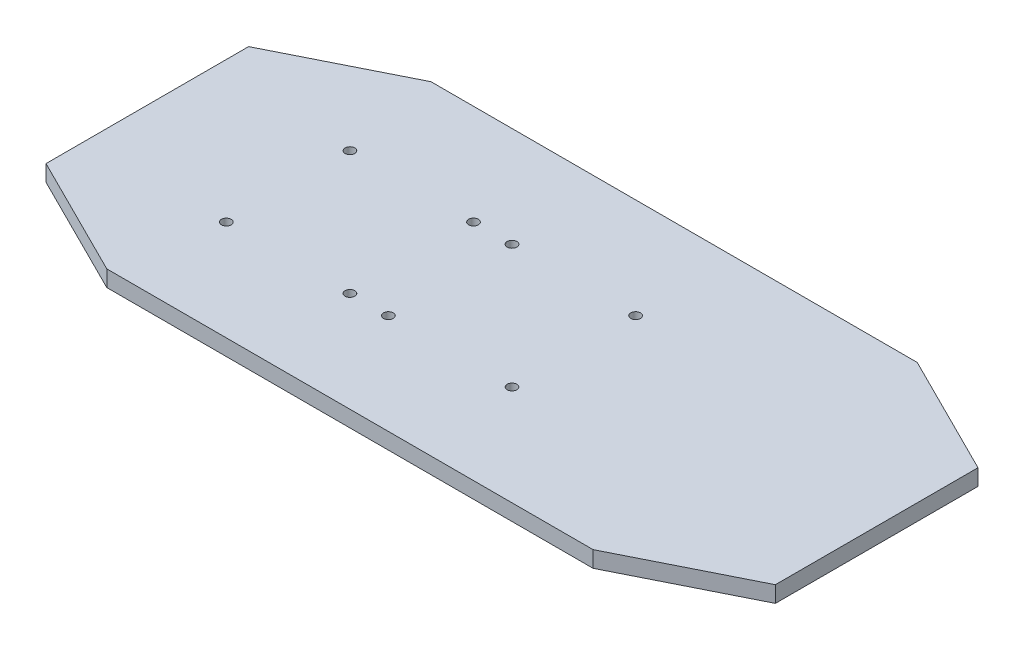
SolidWorks part; units mm, degrees
material "Pin"
ref_plane "Plan de face" through (0, 0, 0) normal (0, 0, 1) x (1, 0, 0)
ref_plane "Plan de dessus" through (0, 0, 0) normal (0, 1, 0) x (1, 0, 0)
ref_plane "Plan de droite" through (0, 0, 0) normal (1, 0, 0) x (0, 0, -1)
sketch "Esquisse1" plane through (0, 0, 0) normal (0, 1, 0) x (1, 0, 0)
  line L1 (0, 0) -> (180, 0)
  line L2 (0, 0) -> (0, 80)
  line L3 (0, 80) -> (180, 80)
  line L4 (180, 0) -> (180, 80)
  dimension "D1" = 180
  dimension "D2" = 80
extrude "Boss.-Extru.1" add sketch "Esquisse1" along normal blind 4
sketch "Esquisse2" plane through (0, 4, 0) normal (0, 1, 0) x (1, 0, 0)
  line L0 (0, 15) -> (30, 0)
  line L1 (0, 80) -> (0, 0) construction
  line L2 (0, 0) -> (180, 0) construction
  line L3 (30, 0) -> (0, 0)
  line L4 (0, 0) -> (0, 15)
  line L5 (30, 80) -> (0, 65)
  line L6 (180, 80) -> (0, 80) construction
  line L7 (0, 65) -> (0, 80)
  line L8 (0, 80) -> (30, 80)
  line L9 (150, 80) -> (180, 80)
  line L10 (180, 80) -> (180, 65)
  line L11 (180, 0) -> (180, 80) construction
  line L12 (180, 65) -> (150, 80)
  line L13 (180, 15) -> (150, 0)
  line L14 (150, 0) -> (180, 0)
  line L15 (180, 0) -> (180, 15)
  dimension "D1" = 30
  dimension "D2" = 15
  dimension "D3" = 30
  dimension "D4" = 15
  dimension "D5" = 15
  dimension "D6" = 30
  dimension "D7" = 30
  dimension "D8" = 15
extrude "Enlèv. mat.-Extru.1" cut sketch "Esquisse2" against normal blind 4
hole_wizard "Dégagement M22" positions "Esquisse9" profile "Esquisse10" size "M2" standard "ISO" slot yes end condition through all
sketch "Esquisse9" plane through (0, 4, 0) normal (0, 1, 0) x (1, 0, 0)
  point P0 (74.75, 55.25)
  point P3 (105.25, 55.25)
  point P6 (105.25, 24.75)
  point P9 (74.75, 24.75)
sketch "Esquisse10" plane through (74.75, 4, -55.25) normal (1, 0, 0) x (0, 0, 1)
  line L0 (0, 0) -> (0, 4)
  line L1 (0, 4) -> (1.2, 4)
  line L2 (1.2, 4) -> (1.2, 0)
  line L5 (1.2, 0) -> (0, 0)
  line L11 (0, -6.35) -> (0, 107.95) construction
  dimension "Diamètre du perçage jusqu'au prochain" = 2.4
  dimension "Profondeur du perçage jusqu'au prochain" = 4
hole_wizard "Dégagement M23" positions "Esquisse11" profile "Esquisse12" size "M2" standard "ISO" slot yes end condition through all
sketch "Esquisse11" plane through (0, 4, 0) normal (0, 1, 0) x (1, 0, 0)
  point P0 (34.75, 24.75)
  point P3 (65.25, 24.75)
  point P6 (65.25, 55.25)
  point P9 (34.75, 55.25)
sketch "Esquisse12" plane through (34.75, 4, -24.75) normal (1, 0, 0) x (0, 0, 1)
  line L0 (0, 0) -> (0, 4)
  line L1 (0, 4) -> (1.2, 4)
  line L2 (1.2, 4) -> (1.2, 0)
  line L5 (1.2, 0) -> (0, 0)
  line L11 (0, -6.35) -> (0, 107.95) construction
  dimension "Diamètre du perçage jusqu'au prochain" = 2.4
  dimension "Profondeur du perçage jusqu'au prochain" = 4
equation "\"D8@Esquisse2\"=\"D2@Esquisse2\""
equation "\"D5@Esquisse2\"=\"D2@Esquisse2\""
equation "\"D4@Esquisse2\"=\"D2@Esquisse2\""
